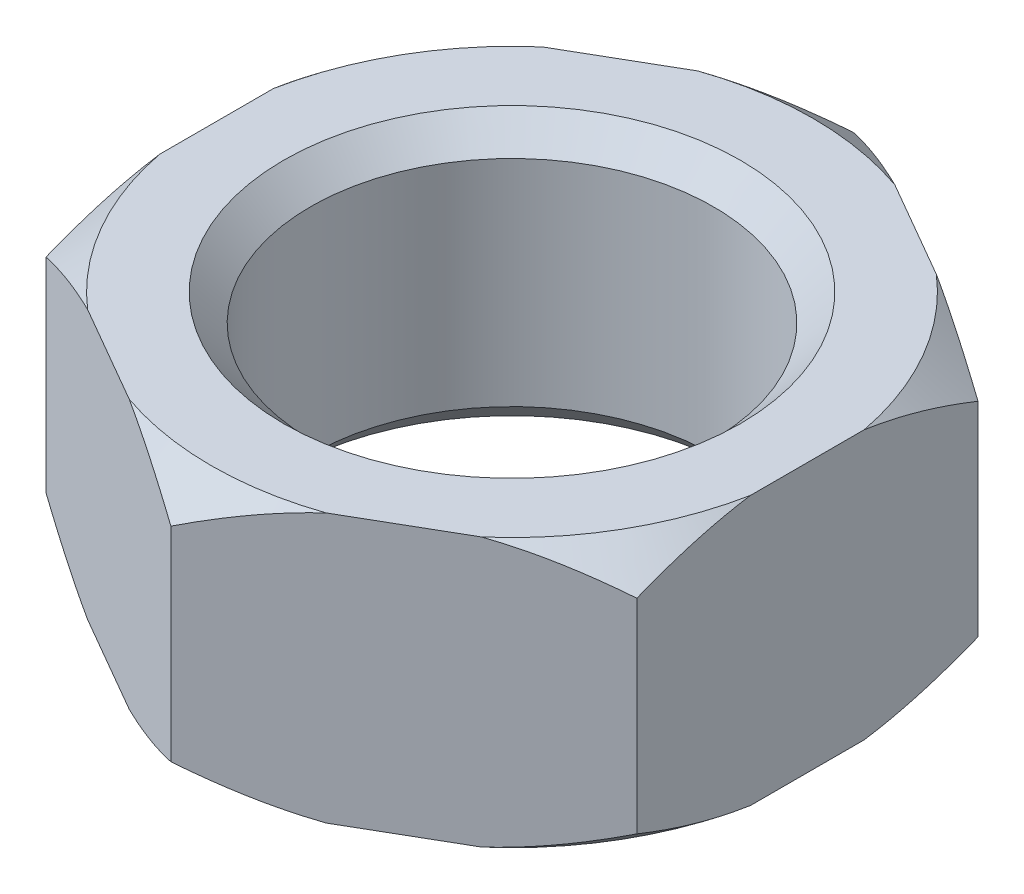
SolidWorks part; units mm, degrees
ref_plane "Front Plane" through (0, 0, 0) normal (0, 0, 1) x (1, 0, 0)
ref_plane "Top Plane" through (0, 0, 0) normal (0, 1, 0) x (1, 0, 0)
ref_plane "Right Plane" through (0, 0, 0) normal (1, 0, 0) x (0, 0, -1)
sketch "Sketch3" plane through (0, 0, 0) normal (0, 1, 0) x (1, 0, 0)
  line L1 (-11, 6.3509) -> (-11, -6.3509)
  line L2 (-11, -6.3509) -> (0, -12.7017)
  line L3 (0, -12.7017) -> (11, -6.3509)
  line L4 (11, -6.3509) -> (11, 6.3509)
  line L5 (11, 6.3509) -> (0, 12.7017)
  line L6 (0, 12.7017) -> (-11, 6.3509)
  circle A0 centre (0, 0) radius 11 construction
  point P1 (0, 0)
  point P10 (0, 0)
  dimension "D1" = 22
extrude "Boss-Extrude1" add sketch "Sketch3" along normal blind 10
sketch "Sketch4" plane through (0, 10, 0) normal (0, 1, 0) x (1, 0, 0)
  circle A0 centre (0, 0) radius 7.5
  dimension "D1" = 15
extrude "Cut-Extrude1" cut sketch "Sketch4" against normal through all
cosmetic thread "Cosmetic Thread1" parameters "D1"=5, "D2"=18
chamfer "Chamfer1" distance 1 angle 45 2 edges at (0, 10, 7.5) (0, 0, 7.5)
sketch "Sketch5" plane through (0, 0, 0) normal (1, 0, 0) x (0, 0, -1)
  line L0 (0, 13.1747) -> (0, -2.9227) construction
  line L1 (-12.7017, 10) -> (-12.7017, 8.8)
  line L2 (-12.7017, 10) -> (-12.7017, 0) construction
  line L3 (-12.7017, 8.8) -> (-11.2017, 10)
  line L4 (-12.7017, 10) -> (-6.3509, 10) construction
  line L5 (-11.2017, 10) -> (-12.7017, 10)
  line L6 (-12.7017, 0) -> (-12.7017, 1.2)
  line L7 (-12.7017, 1.2) -> (-11.2017, 0)
  line L8 (-12.7017, 0) -> (-6.3509, 0) construction
  line L9 (-11.2017, 0) -> (-12.7017, 0)
  dimension "D1" = 1.5
  dimension "D2" = 1.2
  dimension "D3" = 1.2
  dimension "D4" = 1.5
revolve "Cut-Revolve1" cut sketch "Sketch5" angle 360 about L0
